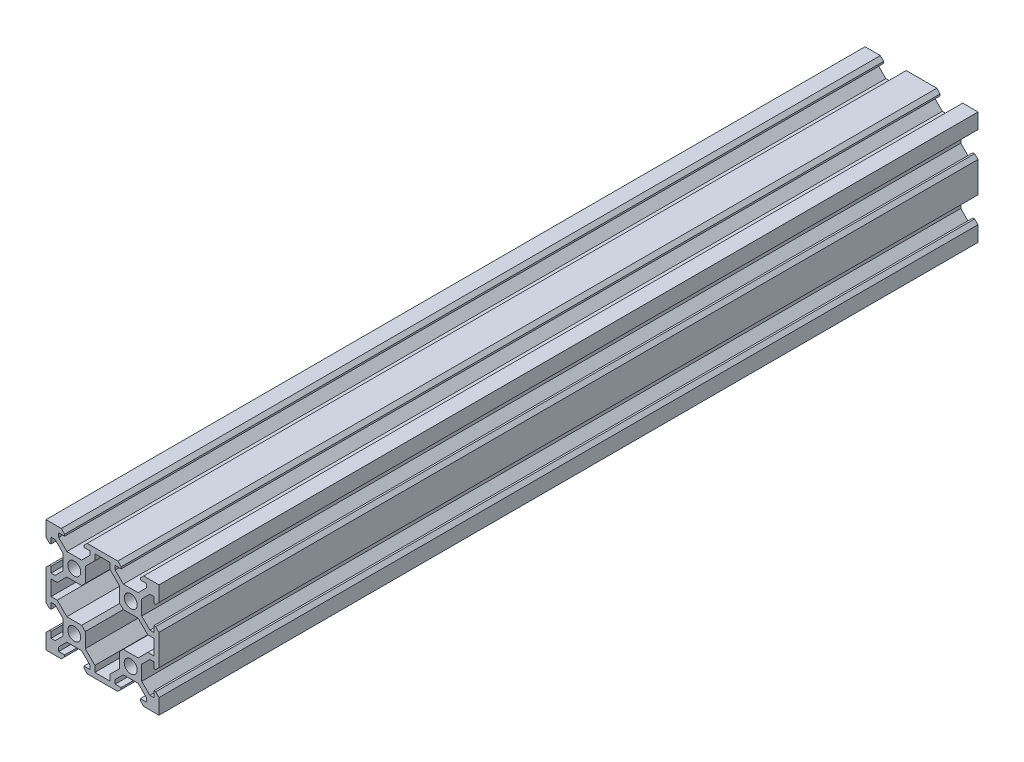
SolidWorks part; units mm, degrees
ref_plane "Front Plane" through (0, 0, 0) normal (0, 0, 1) x (1, 0, 0)
ref_plane "Top Plane" through (0, 0, 0) normal (0, 1, 0) x (1, 0, 0)
ref_plane "Right Plane" through (0, 0, 0) normal (1, 0, 0) x (0, 0, -1)
sketch "Sketch1" plane through (0, 0, 0) normal (0, 0, 1) x (1, 0, 0)
  line L1 (0, 0) -> (40, 0)
  line L2 (0, 0) -> (0, 40)
  line L3 (0, 40) -> (40, 40)
  line L4 (40, 0) -> (40, 40)
  dimension "D1" = 40
extrude "Boss-Extrude1" add sketch "Sketch1" against normal blind 290
sketch "Sketch2" plane through (0, 0, 0) normal (0, 0, 1) x (1, 0, 0)
  line L0 (0, 20) -> (40, 20) construction
  line L1 (0, 40) -> (0, 0) construction
  line L2 (40, 0) -> (40, 40) construction
  line L3 (20, 40) -> (20, 0) construction
  line L4 (40, 40) -> (0, 40) construction
  line L5 (0, 0) -> (40, 0) construction
  line L6 (6.605, 38.815) -> (6.605, 38.2)
  line L7 (6.605, 38.2) -> (4.5, 38.2)
  line L8 (4.5, 38.2) -> (4.5, 36.7728)
  line L9 (4.5, 36.7728) -> (7.3728, 33.9)
  line L10 (7.3728, 33.9) -> (12.6272, 33.9)
  line L11 (12.6272, 33.9) -> (15.5, 36.7728)
  line L12 (15.5, 36.7728) -> (15.5, 38.2)
  line L13 (15.5, 38.2) -> (13.395, 38.2)
  line L14 (13.395, 38.2) -> (13.395, 38.815)
  line L16 (6.605, 38.815) -> (5.42, 40)
  line L17 (13.395, 38.815) -> (14.58, 40)
  line L18 (14.58, 40) -> (5.42, 40)
  line L19 (26.605, 38.815) -> (25.42, 40)
  line L20 (26.605, 38.2) -> (26.605, 38.815)
  line L21 (24.5, 38.2) -> (26.605, 38.2)
  line L22 (24.5, 36.7728) -> (24.5, 38.2)
  line L23 (27.3728, 33.9) -> (24.5, 36.7728)
  line L24 (32.6272, 33.9) -> (27.3728, 33.9)
  line L25 (35.5, 36.7728) -> (32.6272, 33.9)
  line L26 (35.5, 38.2) -> (35.5, 36.7728)
  line L27 (33.395, 38.2) -> (35.5, 38.2)
  line L28 (33.395, 38.815) -> (33.395, 38.2)
  line L29 (33.395, 38.815) -> (34.58, 40)
  line L30 (25.42, 40) -> (34.58, 40)
  line L31 (26.605, 1.8) -> (26.605, 1.185)
  line L32 (24.5, 1.8) -> (26.605, 1.8)
  line L33 (24.5, 3.2272) -> (24.5, 1.8)
  line L34 (27.3728, 6.1) -> (24.5, 3.2272)
  line L35 (32.6272, 6.1) -> (27.3728, 6.1)
  line L36 (35.5, 3.2272) -> (32.6272, 6.1)
  line L37 (35.5, 1.8) -> (35.5, 3.2272)
  line L38 (33.395, 1.8) -> (35.5, 1.8)
  line L39 (33.395, 1.185) -> (33.395, 1.8)
  line L40 (33.395, 1.185) -> (34.58, 0)
  line L41 (25.42, 0) -> (34.58, 0)
  line L42 (26.605, 1.185) -> (25.42, 0)
  line L43 (13.395, 1.185) -> (14.58, 0)
  line L44 (13.395, 1.8) -> (13.395, 1.185)
  line L45 (15.5, 1.8) -> (13.395, 1.8)
  line L46 (15.5, 3.2272) -> (15.5, 1.8)
  line L47 (12.6272, 6.1) -> (15.5, 3.2272)
  line L48 (7.3728, 6.1) -> (12.6272, 6.1)
  line L49 (4.5, 3.2272) -> (7.3728, 6.1)
  line L50 (4.5, 1.8) -> (4.5, 3.2272)
  line L51 (6.605, 1.8) -> (4.5, 1.8)
  line L52 (6.605, 1.185) -> (6.605, 1.8)
  line L53 (6.605, 1.185) -> (5.42, 0)
  line L54 (14.58, 0) -> (5.42, 0)
  line L55 (0, 0) -> (40, 40) construction
  line L56 (1.8, 13.395) -> (1.185, 13.395)
  line L57 (1.8, 15.5) -> (1.8, 13.395)
  line L58 (3.2272, 15.5) -> (1.8, 15.5)
  line L59 (6.1, 12.6272) -> (3.2272, 15.5)
  line L60 (6.1, 7.3728) -> (6.1, 12.6272)
  line L61 (3.2272, 4.5) -> (6.1, 7.3728)
  line L62 (1.8, 4.5) -> (3.2272, 4.5)
  line L63 (1.8, 6.605) -> (1.8, 4.5)
  line L64 (1.185, 6.605) -> (1.8, 6.605)
  line L65 (1.185, 6.605) -> (0, 5.42)
  line L66 (0, 14.58) -> (0, 5.42)
  line L67 (1.185, 13.395) -> (0, 14.58)
  line L68 (0, 40) -> (40, 0) construction
  line L69 (1.185, 26.605) -> (0, 25.42)
  line L70 (1.8, 26.605) -> (1.185, 26.605)
  line L71 (1.8, 24.5) -> (1.8, 26.605)
  line L72 (3.2272, 24.5) -> (1.8, 24.5)
  line L73 (6.1, 27.3728) -> (3.2272, 24.5)
  line L74 (6.1, 32.6272) -> (6.1, 27.3728)
  line L75 (3.2272, 35.5) -> (6.1, 32.6272)
  line L76 (1.8, 35.5) -> (3.2272, 35.5)
  line L77 (1.8, 33.395) -> (1.8, 35.5)
  line L78 (1.185, 33.395) -> (1.8, 33.395)
  line L79 (1.185, 33.395) -> (0, 34.58)
  line L80 (0, 25.42) -> (0, 34.58)
  line L81 (38.2, 15.5) -> (38.2, 13.395)
  line L82 (36.7728, 15.5) -> (38.2, 15.5)
  line L83 (33.9, 12.6272) -> (36.7728, 15.5)
  line L84 (33.9, 7.3728) -> (33.9, 12.6272)
  line L85 (36.7728, 4.5) -> (33.9, 7.3728)
  line L86 (38.2, 4.5) -> (36.7728, 4.5)
  line L87 (38.2, 6.605) -> (38.2, 4.5)
  line L88 (38.815, 6.605) -> (38.2, 6.605)
  line L89 (38.815, 6.605) -> (40, 5.42)
  line L90 (40, 14.58) -> (40, 5.42)
  line L91 (38.815, 13.395) -> (40, 14.58)
  line L92 (38.2, 13.395) -> (38.815, 13.395)
  line L93 (38.2, 26.605) -> (38.815, 26.605)
  line L94 (38.2, 24.5) -> (38.2, 26.605)
  line L95 (36.7728, 24.5) -> (38.2, 24.5)
  line L96 (33.9, 27.3728) -> (36.7728, 24.5)
  line L97 (33.9, 32.6272) -> (33.9, 27.3728)
  line L98 (36.7728, 35.5) -> (33.9, 32.6272)
  line L99 (38.2, 35.5) -> (36.7728, 35.5)
  line L100 (38.2, 33.395) -> (38.2, 35.5)
  line L101 (38.815, 33.395) -> (38.2, 33.395)
  line L102 (38.815, 33.395) -> (40, 34.58)
  line L103 (40, 25.42) -> (40, 34.58)
  line L104 (38.815, 26.605) -> (40, 25.42)
  circle A0 centre (10, 30) radius 2.3
  circle A2 centre (30, 30) radius 2.3
  circle A3 centre (30, 10) radius 2.3
  circle A4 centre (10, 10) radius 2.3
  point P22 (10, 40)
  point P33 (10, 33.9)
  dimension "D1" = 4.6
  dimension "D2" = 20
  dimension "D3" = 20
  dimension "D4" = 4.3
  dimension "D5" = 6.79
  dimension "D6" = 9.16
  dimension "D7" = 11
  dimension "D8" = 90
  dimension "D9" = 1.8
  dimension "D10" = 1.8
extrude "Cut-Extrude1" cut sketch "Sketch2" against normal up to surface (290 mm away) up to face at (20, 20, -290)
sketch "Sketch3" plane through (0, 0, 0) normal (0, 0, 1) x (1, 0, 0)
  line L0 (17.3, 38.2) -> (22.7, 38.2)
  line L1 (0, 20) -> (40, 20) construction
  line L2 (0, 25.42) -> (0, 14.58) construction
  line L3 (40, 14.58) -> (40, 25.42) construction
  line L4 (1.8, 22.7) -> (1.8, 17.3)
  line L5 (12.6272, 13.9) -> (13.9, 12.6272)
  line L6 (13.9, 12.6272) -> (13.9, 7.3728)
  line L7 (7.3728, 13.9) -> (12.6272, 13.9)
  line L8 (13.9, 7.3728) -> (17.3, 3.9728)
  line L9 (17.3, 3.9728) -> (17.3, 1.8)
  line L10 (1.8, 17.3) -> (3.9728, 17.3)
  line L11 (3.9728, 17.3) -> (7.3728, 13.9)
  line L12 (17.3, 1.8) -> (22.7, 1.8)
  line L13 (27.3728, 26.1) -> (26.1, 27.3728)
  line L14 (26.1, 27.3728) -> (26.1, 32.6272)
  line L15 (32.6272, 26.1) -> (27.3728, 26.1)
  line L16 (26.1, 32.6272) -> (22.7, 36.0272)
  line L17 (22.7, 36.0272) -> (22.7, 38.2)
  line L18 (38.2, 22.7) -> (36.0272, 22.7)
  line L19 (36.0272, 22.7) -> (32.6272, 26.1)
  line L20 (36.0272, 17.3) -> (32.6272, 13.9)
  line L21 (38.2, 17.3) -> (36.0272, 17.3)
  line L22 (22.7, 3.9728) -> (22.7, 1.8)
  line L23 (26.1, 7.3728) -> (22.7, 3.9728)
  line L24 (32.6272, 13.9) -> (27.3728, 13.9)
  line L25 (26.1, 12.6272) -> (26.1, 7.3728)
  line L26 (27.3728, 13.9) -> (26.1, 12.6272)
  line L27 (38.2, 22.7) -> (38.2, 17.3)
  line L117 (3.9728, 22.7) -> (7.3728, 26.1)
  line L118 (1.8, 22.7) -> (3.9728, 22.7)
  line L119 (3.9728, 22.7) -> (7.3728, 26.1)
  line L120 (1.8, 22.7) -> (3.9728, 22.7)
  line L134 (20, 40) -> (20, 0) construction
  line L135 (25.42, 40) -> (14.58, 40) construction
  line L136 (17.3, 36.0272) -> (17.3, 38.2)
  line L137 (13.9, 32.6272) -> (17.3, 36.0272)
  line L138 (17.3, 36.0272) -> (17.3, 38.2)
  line L139 (13.9, 32.6272) -> (17.3, 36.0272)
  line L140 (14.58, 0) -> (25.42, 0) construction
  line L141 (7.3728, 26.1) -> (12.6272, 26.1)
  line L142 (13.9, 27.3728) -> (13.9, 32.6272)
  line L155 (12.6272, 26.1) -> (13.9, 27.3728)
  circle A2 centre (10, 30) radius 2.3 construction
  circle A3 centre (10, 30) radius 2.3 construction
  circle A4 centre (10, 10) radius 2.3 construction
  circle A5 centre (30, 10) radius 2.3 construction
  circle A6 centre (30, 30) radius 2.3 construction
  point P24 (10, 26.1)
  point P25 (38.2, 20)
  point P38 (1.8, 20)
  point P52 (20, 1.8)
  point P59 (20, 38.2)
  dimension "D5" = 135
  dimension "D1" = 1.8
  dimension "D3" = 1.8
extrude "Cut-Extrude2" cut sketch "Sketch3" against normal up to surface (290 mm away) up to face at (20, 20, -290)
